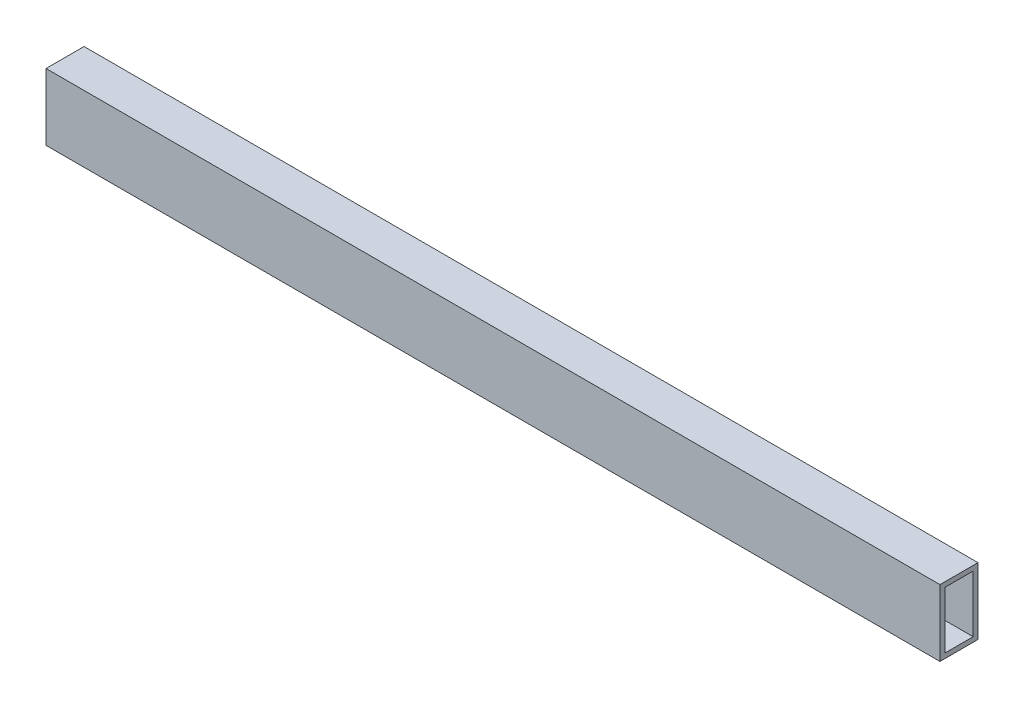
SolidWorks part; units mm, degrees
ref_plane "Front Plane" through (0, 0, 0) normal (0, 0, 1) x (1, 0, 0)
ref_plane "Top Plane" through (0, 0, 0) normal (0, 1, 0) x (1, 0, 0)
ref_plane "Right Plane" through (0, 0, 0) normal (1, 0, 0) x (0, 0, -1)
sketch "Sketch1" plane through (0, 0, 0) normal (0, 0, 1) x (1, 0, 0)
  line L1 (-9470.2182, 3159.1314) -> (-8873.3182, 3159.1314)
  line L2 (-9470.2182, 3159.1314) -> (-9470.2182, 3114.6814)
  line L3 (-9470.2182, 3114.6814) -> (-8873.3182, 3114.6814)
  line L4 (-8873.3182, 3159.1314) -> (-8873.3182, 3114.6814)
  dimension "D1" = 44.45
  dimension "D2" = 596.9
extrude "Boss-Extrude1" add sketch "Sketch1" along normal blind 25.4
sketch "Sketch2" plane through (-8873.3182, 0, 0) normal (1, 0, 0) x (0, 0, -1)
  line L0 (-25.4, 3159.1314) -> (0, 3159.1314) construction
  line L1 (-22.1615, 3155.8929) -> (-3.2385, 3155.8929)
  line L2 (-22.1615, 3155.8929) -> (-22.1615, 3117.9199)
  line L3 (-22.1615, 3117.9199) -> (-3.2385, 3117.9199)
  line L4 (-3.2385, 3155.8929) -> (-3.2385, 3117.9199)
  line L5 (0, 3114.6814) -> (0, 3159.1314) construction
  line L6 (-25.4, 3114.6814) -> (-25.4, 3159.1314) construction
  line L7 (-25.4, 3114.6814) -> (0, 3114.6814) construction
  dimension "D1" = 3.2385
  dimension "D2" = 3.2385
  dimension "D3" = 3.2385
  dimension "D4" = 3.2385
extrude "Cut-Extrude1" cut sketch "Sketch2" against normal blind 599.44
